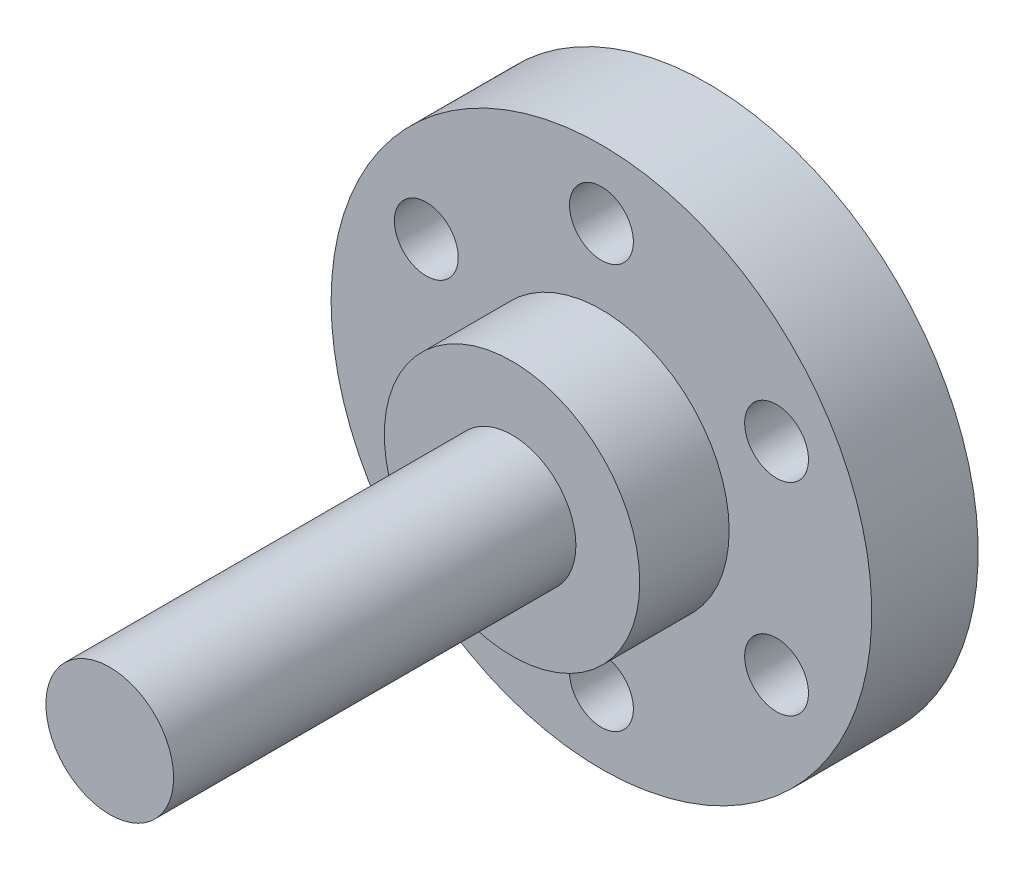
SolidWorks part; units mm, degrees
material "1060 Alloy"
ref_plane "Front Plane" through (0, 0, 0) normal (0, 0, 1) x (1, 0, 0)
ref_plane "Top Plane" through (0, 0, 0) normal (0, 1, 0) x (1, 0, 0)
ref_plane "Right Plane" through (0, 0, 0) normal (1, 0, 0) x (0, 0, -1)
sketch "Sketch1" plane through (0, 0, 0) normal (0, 0, 1) x (1, 0, 0)
  circle A0 centre (0, 0) radius 3
  dimension "D1" = 6
extrude "Boss-Extrude1" add sketch "Sketch1" along normal blind 29
ref_plane "Plane1" through (0, 0, 8) normal (0, 0, 1) x (1, 0, 0)
sketch "Sketch2" plane through (0, 0, 8) normal (0, 0, 1) x (1, 0, 0)
  circle A0 centre (0, 0) radius 6
  dimension "D1" = 12
  dimension "D2" = 12
extrude "Boss-Extrude2" add sketch "Sketch2" against normal blind 2.1
sketch "Sketch3" plane through (0, 0, 5.9) normal (0, 0, -1) x (-1, 0, 0)
  circle A0 centre (0, 0) radius 12.7
  dimension "D1" = 25.4
extrude "Boss-Extrude3" add sketch "Sketch3" along normal blind 5
sketch "Sketch4" plane through (0, 0, 8) normal (0, 0, 1) x (1, 0, 0)
  circle A0 centre (0, 0) radius 6
extrude "Boss-Extrude4" add sketch "Sketch4" along normal blind 2.1
sketch "Sketch10" plane through (0, 0, 0.9) normal (0, 0, -1) x (-1, 0, 0)
  circle A0 centre (8.2272, 4.75) radius 1.5
  circle A1 centre (0, 9.5) radius 1.5
  circle A2 centre (8.2272, -4.75) radius 1.5
  circle A3 centre (0, -9.5) radius 1.5
  circle A4 centre (-8.2272, -4.75) radius 1.5
  circle A5 centre (-8.2272, 4.75) radius 1.5
  point P15 (0, 0)
  dimension "D1" = 6
  dimension "D2" = 3
extrude "Cut-Extrude1" cut sketch "Sketch10" against normal blind 10
